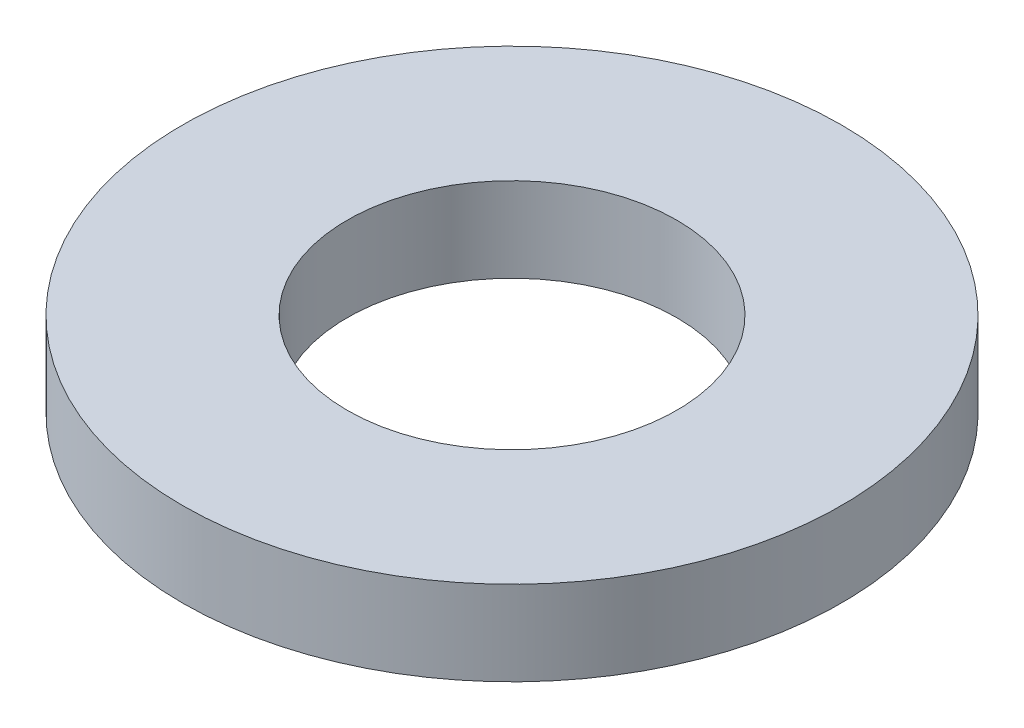
SolidWorks part; units mm, degrees
ref_plane "前视基准面" through (0, 0, 0) normal (0, 0, 1) x (1, 0, 0)
ref_plane "上视基准面" through (0, 0, 0) normal (0, 1, 0) x (1, 0, 0)
ref_plane "右视基准面" through (0, 0, 0) normal (1, 0, 0) x (0, 0, -1)
sketch "草图1" plane through (0, 0, 0) normal (0, 0, 1) x (1, 0, 0)
  line L0 (1.9812, 1.016) -> (1.9812, 0)
  line L1 (1.9812, 0) -> (3.9624, 0)
  line L2 (3.9624, 0) -> (3.9624, 1.016)
  line L3 (3.9624, 1.016) -> (1.9812, 1.016)
  line L4 (0, 1.016) -> (0, 0) construction
revolve "旋转1" add sketch "草图1" angle 360 about L4
